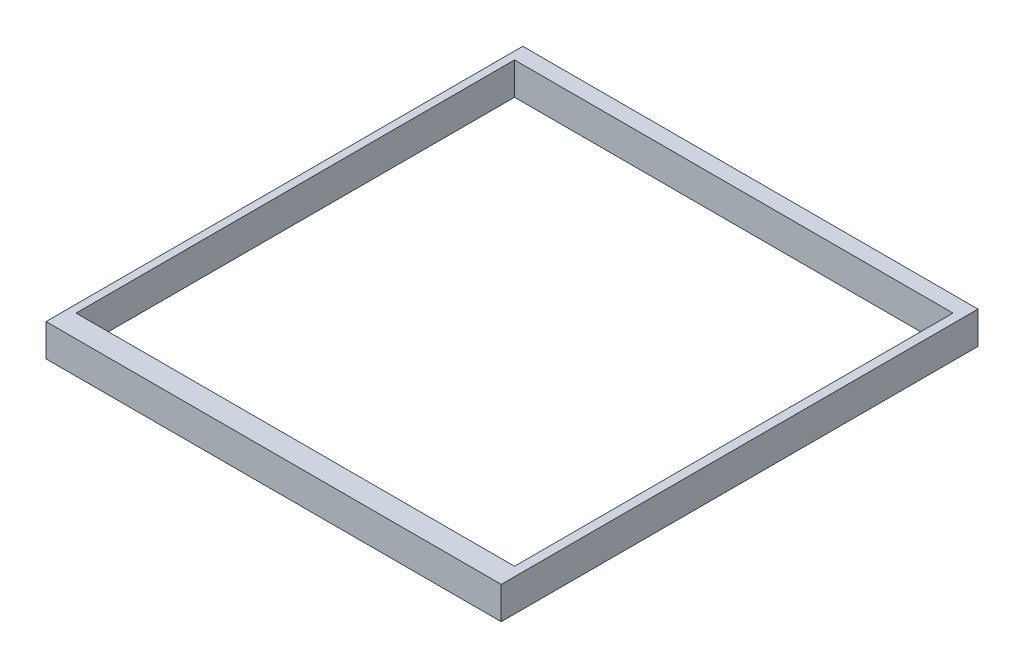
SolidWorks part; units mm, degrees
ref_plane "Front Plane" through (0, 0, 0) normal (0, 0, 1) x (1, 0, 0)
ref_plane "Top Plane" through (0, 0, 0) normal (0, 1, 0) x (1, 0, 0)
ref_plane "Right Plane" through (0, 0, 0) normal (1, 0, 0) x (0, 0, -1)
sketch "Sketch1" plane through (214.7108, 0, 138.124) normal (0, 1, 0) x (1, 0, 0)
  line L0 (38.9883, -1817.2187) -> (38.9883, -22.7813)
  line L1 (11.4359, 38.5955) -> (1911.4359, 38.5955)
  line L2 (11.4359, 38.5955) -> (11.4359, -1951.4045)
  line L3 (11.4359, -1951.4045) -> (1911.4359, -1951.4045)
  line L4 (1911.4359, 38.5955) -> (1911.4359, -1951.4045)
  line L5 (38.9883, -1817.2187) -> (1801.0117, -1817.2187)
  line L6 (38.9883, -22.7813) -> (1801.0117, -22.7813)
  line L7 (1801.0117, -1817.2187) -> (1801.0117, -22.7813)
  line L8 (38.9883, -1817.2187) -> (1801.0117, -22.7813) construction
  line L9 (38.9883, -22.7813) -> (1801.0117, -1817.2187) construction
  point P6 (920, -920)
  dimension "D1" = 1900
  dimension "D2" = 1990
extrude "Boss-Extrude1" add sketch "Sketch1" along normal blind 135 contours L2 L3 L4 L1
sketch "Sketch2" plane through (214.7108, 135, 138.124) normal (0, 1, 0) x (1, 0, 0)
  line L0 (43.6199, -1858.058) -> (43.6199, -28.058)
  line L1 (43.6199, -1858.058) -> (1873.6199, -1858.058)
  line L2 (43.6199, -28.058) -> (1873.6199, -28.058)
  line L3 (1873.6199, -1858.058) -> (1873.6199, -28.058)
  line L4 (43.6199, -1858.058) -> (1873.6199, -28.058) construction
  line L5 (43.6199, -28.058) -> (1873.6199, -1858.058) construction
  point P1 (958.6199, -943.058)
  dimension "D1" = 1830
  dimension "D2" = 1830
extrude "Cut-Extrude2" cut sketch "Sketch2" against normal blind 445
sketch "Sketch3" plane through (0, 0, 2089.5284) normal (0, 0, 1) x (1, 0, 0)
